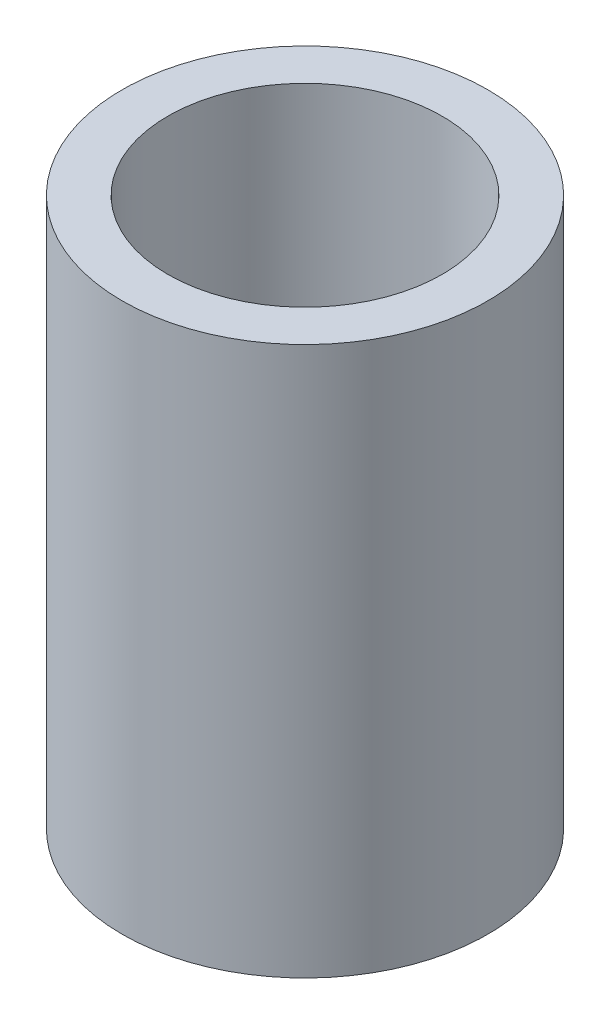
SolidWorks part; units mm, degrees
ref_plane "Front Plane" through (0, 0, 0) normal (0, 0, 1) x (1, 0, 0)
ref_plane "Top Plane" through (0, 0, 0) normal (0, 1, 0) x (1, 0, 0)
ref_plane "Right Plane" through (0, 0, 0) normal (1, 0, 0) x (0, 0, -1)
sketch "Sketch1" plane through (0, 0, 0) normal (0, 1, 0) x (1, 0, 0)
  circle A0 centre (0, 0) radius 12.7
  circle A1 centre (0, 0) radius 9.525
  dimension "D1" = 19.05
  dimension "D2" = 25.4
extrude "Boss-Extrude2" add sketch "Sketch1" along normal blind 38.1
